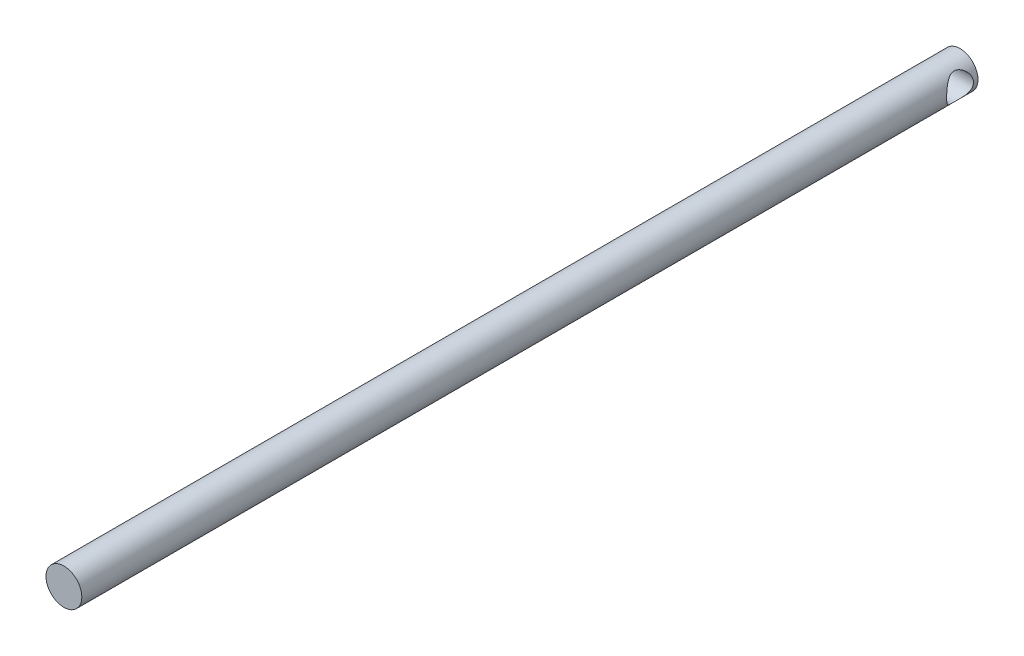
SolidWorks part; units mm, degrees
ref_plane "Front Plane" through (0, 0, 0) normal (0, 0, 1) x (1, 0, 0)
ref_plane "Top Plane" through (0, 0, 0) normal (0, 1, 0) x (1, 0, 0)
ref_plane "Right Plane" through (0, 0, 0) normal (1, 0, 0) x (0, 0, -1)
sketch "Sketch1" plane through (0, 0, 0) normal (0, 0, 1) x (1, 0, 0)
  circle A0 centre (0, 0) radius 10
  dimension "D1" = 20
extrude "Boss-Extrude1" add sketch "Sketch1" along normal blind 500
sketch "Sketch2" plane through (0, 0, 0) normal (1, 0, 0) x (0, 0, -1)
  line L0 (0, -10) -> (0, 10) construction
  circle A0 centre (-10, 0) radius 7.5
  dimension "D1" = 15
  dimension "D2" = 10
extrude "Cut-Extrude1" cut sketch "Sketch2" against normal through all both and the other way through all
